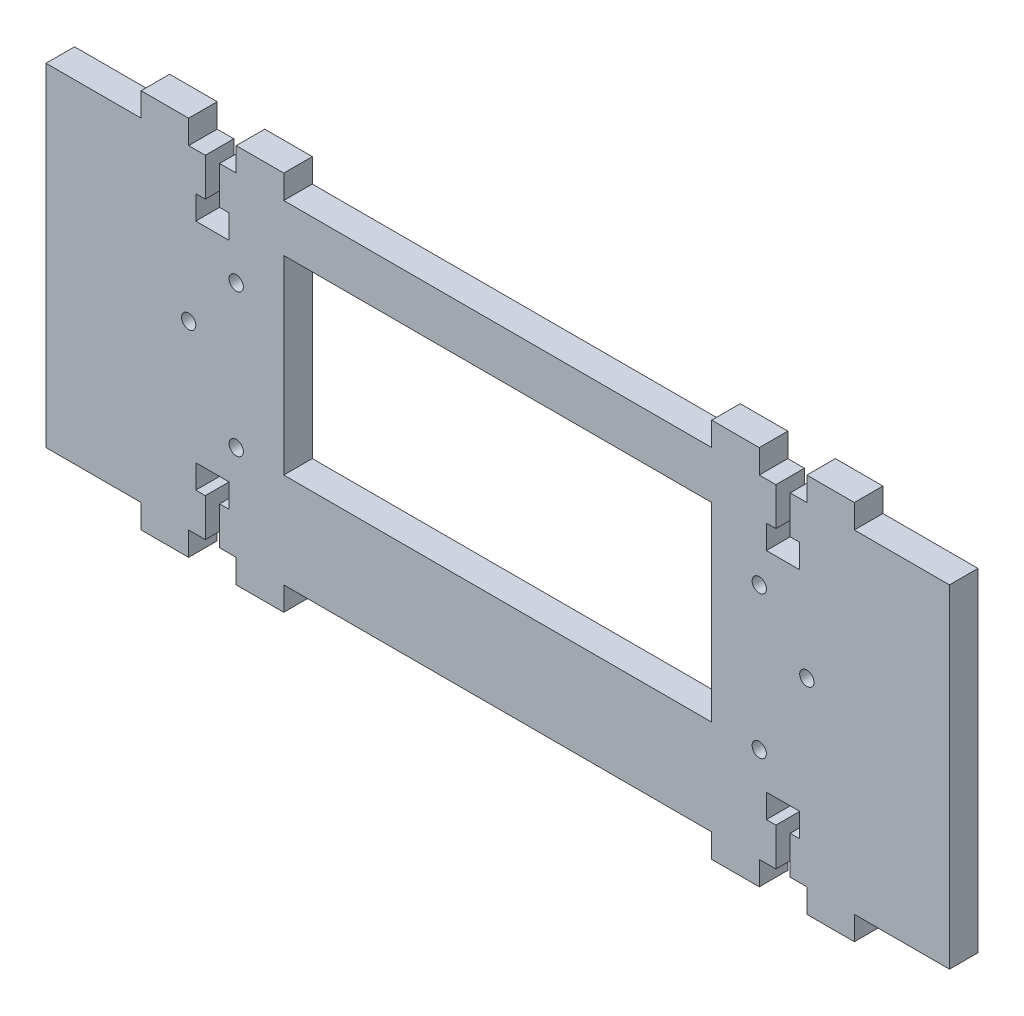
SolidWorks part; units mm, degrees
material "Cedro"
ref_plane "Plano frontal" through (0, 0, 0) normal (0, 0, 1) x (1, 0, 0)
ref_plane "Plano superior" through (0, 0, 0) normal (0, 1, 0) x (1, 0, 0)
ref_plane "Plano direito" through (0, 0, 0) normal (1, 0, 0) x (0, 0, -1)
sketch "Model" plane through (0, 0, 0) normal (0, 0, 1) x (1, 0, 0)
  line L0 (140, -10) -> (140, -50)
  line L1 (140, -50) -> (50, -50)
  line L2 (50, -50) -> (50, -10)
  line L3 (50, -10) -> (140, -10)
  line L4 (36.5, -62) -> (36.5, -70)
  line L5 (36.5, -70) -> (40, -70)
  line L6 (40, -70) -> (40, -75)
  line L7 (40, -75) -> (50, -75)
  line L8 (50, -75) -> (50, -70)
  line L9 (50, -70) -> (140, -70)
  line L10 (140, -70) -> (140, -75)
  line L11 (140, -75) -> (150, -75)
  line L12 (150, -75) -> (150, -70)
  line L13 (150, -70) -> (153.5, -70)
  line L14 (153.5, -70) -> (153.5, -62)
  line L15 (153.5, -62) -> (151.5, -62)
  line L16 (151.5, -62) -> (151.5, -57)
  line L17 (151.5, -57) -> (158.5, -57)
  line L18 (158.5, -57) -> (158.5, -62)
  line L19 (158.5, -62) -> (156.5, -62)
  line L20 (156.5, -62) -> (156.5, -70)
  line L21 (156.5, -70) -> (160, -70)
  line L22 (160, -70) -> (160, -75)
  line L23 (160, -75) -> (170, -75)
  line L24 (170, -75) -> (170, -70)
  line L25 (170, -70) -> (190, -70)
  line L26 (190, -70) -> (190, 0)
  line L27 (190, 0) -> (170, 0)
  line L28 (170, 0) -> (170, 5)
  line L29 (170, 5) -> (160, 5)
  line L30 (160, 5) -> (160, 0)
  line L31 (160, 0) -> (156.5, 0)
  line L32 (156.5, 0) -> (156.5, -8)
  line L33 (156.5, -8) -> (158.5, -8)
  line L34 (158.5, -8) -> (158.5, -13)
  line L35 (158.5, -13) -> (151.5, -13)
  line L36 (151.5, -13) -> (151.5, -8)
  line L37 (151.5, -8) -> (153.5, -8)
  line L38 (153.5, -8) -> (153.5, 0)
  line L39 (153.5, 0) -> (150, 0)
  line L40 (150, 0) -> (150, 5)
  line L41 (150, 5) -> (140, 5)
  line L42 (140, 5) -> (140, 0)
  line L43 (140, 0) -> (50, 0)
  line L44 (50, 0) -> (50, 5)
  line L45 (50, 5) -> (40, 5)
  line L46 (40, 5) -> (40, 0)
  line L47 (40, 0) -> (36.5, 0)
  line L48 (36.5, 0) -> (36.5, -8)
  line L49 (36.5, -8) -> (38.5, -8)
  line L50 (38.5, -8) -> (38.5, -13)
  line L51 (38.5, -13) -> (31.5, -13)
  line L52 (31.5, -13) -> (31.5, -8)
  line L53 (31.5, -8) -> (33.5, -8)
  line L54 (33.5, -8) -> (33.5, 0)
  line L55 (33.5, 0) -> (30, 0)
  line L56 (30, 0) -> (30, 5)
  line L57 (30, 5) -> (20, 5)
  line L58 (20, 5) -> (20, 0)
  line L59 (20, 0) -> (0, 0)
  line L60 (0, 0) -> (0, -70)
  line L61 (0, -70) -> (20, -70)
  line L62 (20, -70) -> (20, -75)
  line L63 (20, -75) -> (30, -75)
  line L64 (30, -75) -> (30, -70)
  line L65 (30, -70) -> (33.5, -70)
  line L66 (33.5, -70) -> (33.5, -62)
  line L67 (33.5, -62) -> (31.5, -62)
  line L68 (31.5, -62) -> (31.5, -57)
  line L69 (31.5, -57) -> (38.5, -57)
  line L70 (38.5, -57) -> (38.5, -62)
  line L71 (38.5, -62) -> (36.5, -62)
  circle A0 centre (30, -32) radius 1.5
  circle A1 centre (150, -50) radius 1.5
  circle A2 centre (40, -20) radius 1.5
  circle A3 centre (150, -20) radius 1.5
  circle A4 centre (40, -50) radius 1.5
  circle A5 centre (160, -32) radius 1.5
  dimension "D1" = 70
  dimension "D2" = 20
  dimension "D3" = 10
  dimension "D4" = 7
  dimension "D5" = 10
  dimension "D6" = 90
  dimension "D7" = 10
  dimension "D8" = 10
  dimension "D9" = 20
  dimension "D10" = 70
  dimension "D11" = 20
  dimension "D12" = 10
  dimension "D13" = 10
  dimension "D14" = 90
  dimension "D15" = 10
  dimension "D16" = 10
  dimension "D17" = 20
  dimension "D18" = 13
  dimension "D19" = 5
  dimension "D20" = 5
  dimension "D21" = 8
  dimension "D22" = 5
  dimension "D23" = 5
  dimension "D24" = 7
  dimension "D25" = 10
  dimension "D26" = 3
extrude "Ressalto-extrusão1" add sketch "Model" along normal blind 6
